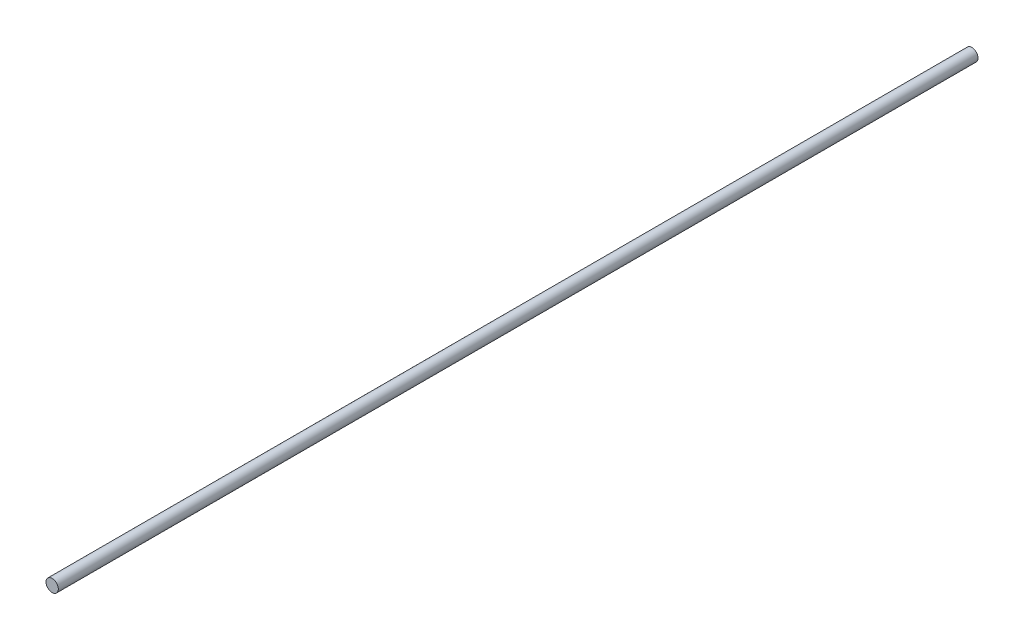
SolidWorks part; units mm, degrees
material "1023 Carbon Steel Sheet (SS)"
ref_plane "Front Plane" through (0, 0, 0) normal (0, 0, 1) x (1, 0, 0)
ref_plane "Top Plane" through (0, 0, 0) normal (0, 1, 0) x (1, 0, 0)
ref_plane "Right Plane" through (0, 0, 0) normal (1, 0, 0) x (0, 0, -1)
sketch "Sketch1" plane through (0, 0, 0) normal (0, 0, 1) x (1, 0, 0)
  circle A0 centre (0, 0) radius 11.049
  dimension "D1" = 22.098
extrude "Boss-Extrude1" add sketch "Sketch1" along normal mid plane 1651
